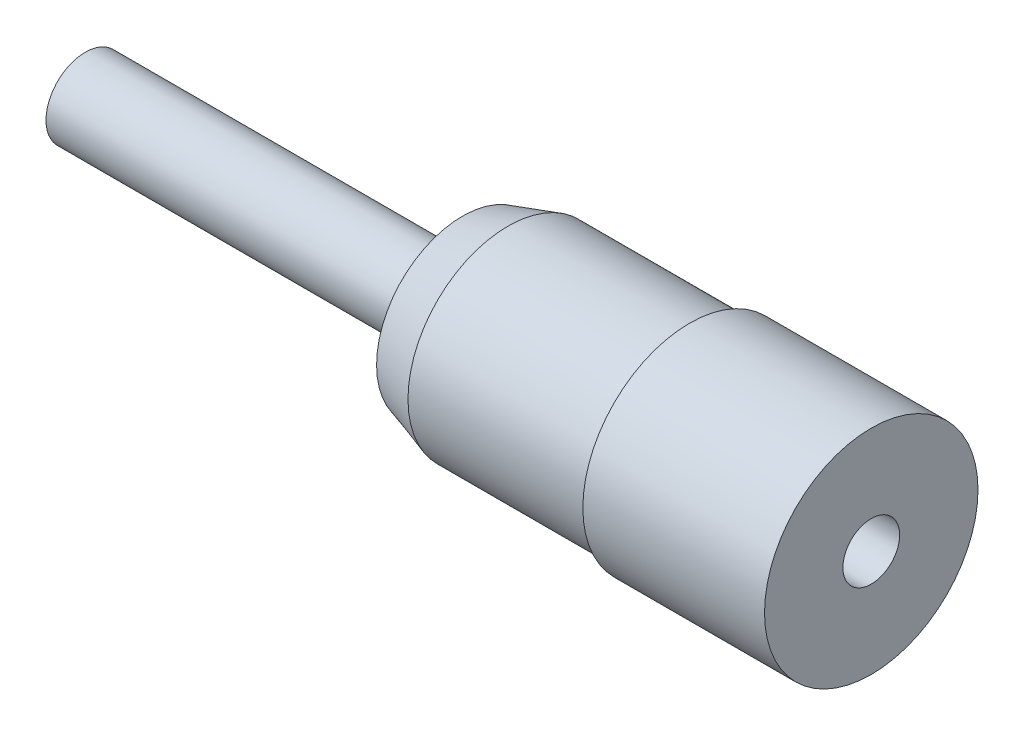
SolidWorks part; units mm, degrees
ref_plane "Front Plane" through (0, 0, 0) normal (0, 0, 1) x (1, 0, 0)
ref_plane "Top Plane" through (0, 0, 0) normal (0, 1, 0) x (1, 0, 0)
ref_plane "Right Plane" through (0, 0, 0) normal (1, 0, 0) x (0, 0, -1)
sketch "Sketch2" plane through (0, 0, 0) normal (0, 0, 1) x (1, 0, 0)
  line L0 (277.539, 63.4078) -> (314.539, 63.3714) construction
  line L1 (276.2601, 76.7069) -> (312.0557, 76.7069) construction
  line L2 (296.0557, 81.1069) -> (303.8557, 81.1069)
  line L3 (303.8557, 81.1069) -> (304.0557, 81.4069)
  line L4 (304.0557, 81.4069) -> (312.0557, 81.4069)
  line L5 (312.0557, 81.4069) -> (312.0557, 79.4069)
  line L6 (294.0557, 80.4888) -> (294.0557, 80.1748)
  line L7 (296.0557, 81.1069) -> (294.0557, 80.4888)
  line L8 (294.0469, 78.4369) -> (309.4469, 78.4369)
  line L9 (277.4469, 76.7069) -> (277.4469, 78.4369)
  line L10 (277.4469, 78.4369) -> (294.0469, 78.4369)
  line L11 (296.101, 80.8069) -> (294.0557, 80.1748)
  line L12 (296.101, 80.8069) -> (304.0162, 80.8069)
  line L13 (304.0162, 80.8069) -> (304.2162, 81.1069)
  line L14 (304.2162, 81.1069) -> (309.4469, 81.1069)
  line L15 (312.0557, 79.4069) -> (312.0557, 76.7069)
  line L16 (314.0469, 76.7069) -> (315.4863, 76.7069) construction
  line L17 (304.2162, 81.1069) -> (312.0557, 81.1069) construction
  line L18 (296.101, 80.8069) -> (294.1443, 80.2021) construction
  line L19 (309.4469, 78.4369) -> (309.4469, 81.1069)
  line L21 (277.4469, 76.7069) -> (312.0557, 76.7069)
  dimension "D6" = 2
  dimension "D1" = 37
  dimension "D2" = 4.7
  dimension "D3" = 4.4
  dimension "D7" = 1.73
  dimension "D8" = 18
  dimension "D9" = 2
  dimension "D10" = 15.4
  dimension "D11" = 0.2
  dimension "D12" = 8
  dimension "D13" = 0.3
revolve "Revolve4" add sketch "Sketch2" angle 360 about L21
hole_wizard "Tap Drill for M3 Tap1" positions "Sketch4" profile "Sketch3" hole size "M3" standard "ISO"
sketch "Sketch4" plane through (312.0557, 0, 0) normal (1, 0, 0) x (0, 0, -1)
  point P0 (0, 76.7069)
sketch "Sketch3" plane through (312.0557, 76.7069, 0) normal (0, 1, 0) x (0, 0, -1)
  line L0 (0, 0) -> (0, 6.2511)
  line L1 (0, 6.2511) -> (1.25, 5.5)
  line L2 (1.25, 5.5) -> (1.25, 0)
  line L5 (1.25, 0) -> (0, 0)
  line L10 (0, 6.2511) -> (-1.25, 5.5) construction
  line L11 (0, -6.35) -> (0, 107.95) construction
  dimension "Hole Dia." = 2.5
  dimension "Hole Depth" = 5.5
  dimension "Drill Angle" = 118
